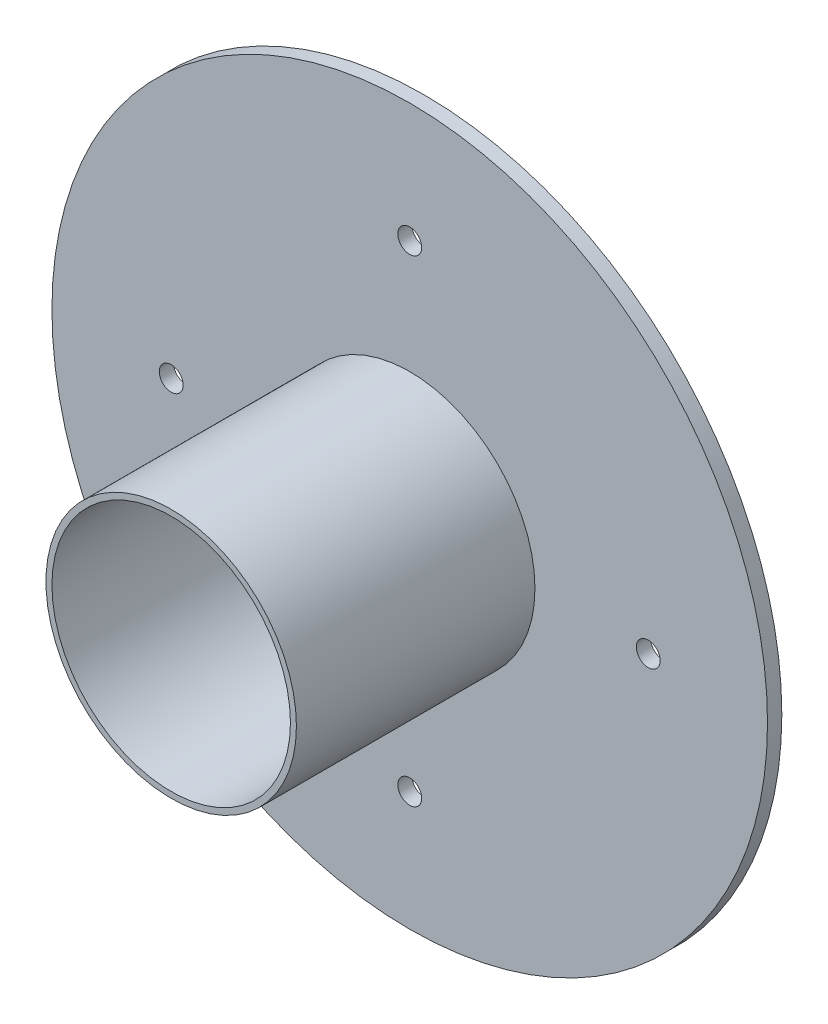
SolidWorks part; units mm, degrees
ref_plane "Front Plane" through (0, 0, 0) normal (0, 0, 1) x (1, 0, 0)
ref_plane "Top Plane" through (0, 0, 0) normal (0, 1, 0) x (1, 0, 0)
ref_plane "Right Plane" through (0, 0, 0) normal (1, 0, 0) x (0, 0, -1)
sketch "Sketch2" plane through (0, 0, 0) normal (0, 0, 1) x (1, 0, 0)
  circle A0 centre (0, 0) radius 150
  dimension "D1" = 300
extrude "Boss-Extrude1" add sketch "Sketch2" along normal blind 6
sketch "Sketch3" plane through (0, 0, 6) normal (0, 0, 1) x (1, 0, 0)
  circle A0 centre (0, 0) radius 50
  circle A1 centre (0, 0) radius 52.5
  dimension "D1" = 100
  dimension "D2" = 105
extrude "Boss-Extrude2" add sketch "Sketch3" along normal blind 100 contours A1 | A0
sketch "Sketch4" plane through (0, 0, 6) normal (0, 0, 1) x (1, 0, 0)
  line L0 (0, 0) -> (150, 0) construction
  circle A0 centre (0, 0) radius 150 construction
  circle A1 centre (100, 0) radius 5
  circle A2 centre (0, -100) radius 5
  circle A3 centre (-100, 0) radius 5
  circle A4 centre (0, 100) radius 5
  dimension "D1" = 100
  dimension "D2" = 4
extrude "Cut-Extrude1" cut sketch "Sketch4" against normal blind 100 contours A4 | L0 A1 | A1 L0 | A2 | A3
